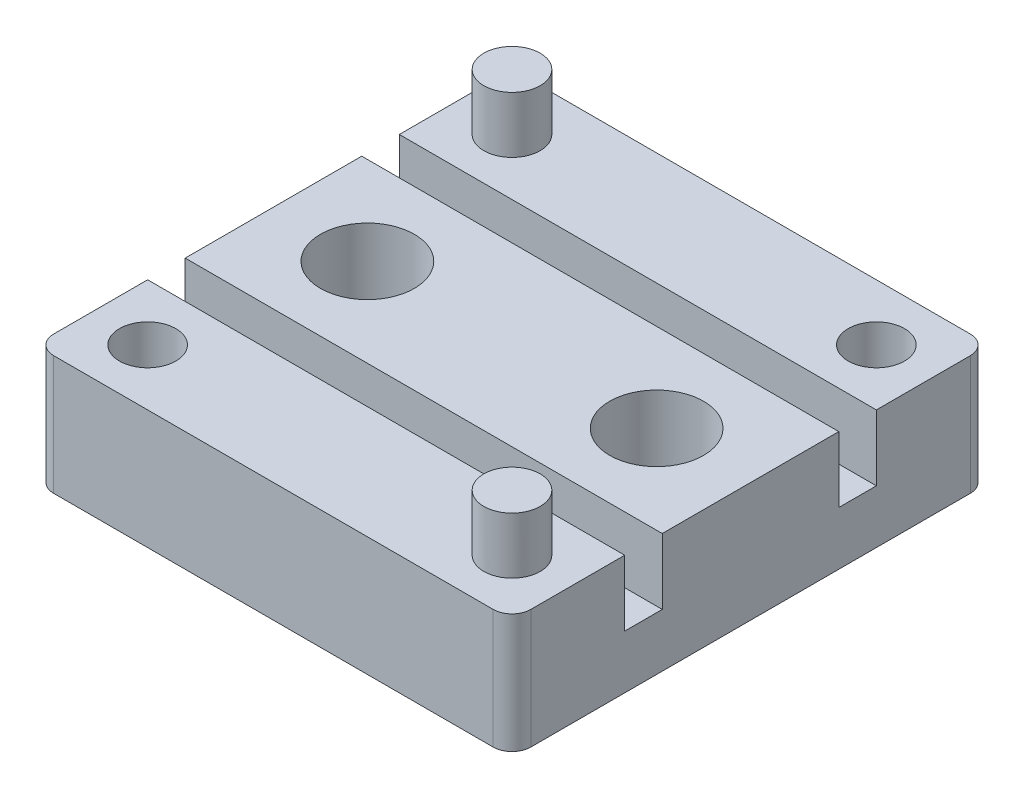
SolidWorks part; units mm, degrees
material "Nylon 101"
ref_plane "Front Plane" through (0, 0, 0) normal (0, 0, 1) x (1, 0, 0)
ref_plane "Top Plane" through (0, 0, 0) normal (0, 1, 0) x (1, 0, 0)
ref_plane "Right Plane" through (0, 0, 0) normal (1, 0, 0) x (0, 0, -1)
sketch "Sketch1" plane through (0, 0, 0) normal (0, 1, 0) x (1, 0, 0)
  line L1 (0, 0) -> (-12.7, 0)
  line L2 (0, 0) -> (0, 12.7)
  line L3 (0, 12.7) -> (-12.7, 12.7)
  line L4 (-12.7, 0) -> (-12.7, 12.7)
  circle A0 centre (-2.5, 6.35) radius 1.25
  circle A1 centre (-10.2, 6.35) radius 1.25
  point P9 (0, 6.35)
  dimension "D3" = 2.5
  dimension "D4" = 2.5
  dimension "D5" = 2.5
  dimension "D1" = 12.7
  dimension "D2" = 12.7
extrude "Boss-Extrude1" add sketch "Sketch1" along normal blind 3.175
sketch "Sketch2" plane through (0, 3.175, 0) normal (0, 1, 0) x (1, 0, 0)
  line L0 (0, 12.7) -> (-12.7, 12.7) construction
  line L1 (-12.7, 12.7) -> (-12.7, 0) construction
  circle A0 centre (-11.2, 11.2) radius 0.75
  dimension "D1" = 1.5
  dimension "D2" = 1.5
  dimension "D3" = 1.5
extrude "Boss-Extrude2" add sketch "Sketch2" along normal blind 1.5
sketch "Sketch3" plane through (0, 3.175, 0) normal (0, 1, 0) x (1, 0, 0)
  line L0 (0, 12.7) -> (-12.7, 12.7) construction
  line L1 (0, 0) -> (0, 12.7) construction
  circle A0 centre (-1.5, 11.2) radius 0.75
  dimension "D1" = 1.5
  dimension "D2" = 1.5
  dimension "D3" = 1.5
extrude "Cut-Extrude1" cut sketch "Sketch3" against normal blind 1.5
ref_plane "Plane2" through (-6.35, 0, -6.35) normal (-0.7071, 0, -0.7071) x (-0.7071, 0, 0.7071)
ref_plane "Plane3" through (0, 0, 0) normal (-0.7071, 0, 0.7071) x (0.7071, 0, 0.7071)
ref_plane "Plane4" through (0, 0, -6.35) normal (0, 0, -1) x (-1, 0, 0)
mirror "Mirror1" about plane through (-6.35, 0, -6.35) normal (-0.7071, 0, -0.7071) of "Boss-Extrude2"
mirror "Mirror2" about plane through (0, 0, 0) normal (-0.7071, 0, 0.7071) of "Cut-Extrude1"
sketch "Sketch4" plane through (0, 3.175, 0) normal (0, 1, 0) x (1, 0, 0)
  line L0 (-12.7, 12.7) -> (-12.7, 0) construction
  line L1 (-12.7, 8.7) -> (0, 8.7)
  line L2 (-12.7, 8.7) -> (-12.7, 9.7)
  line L3 (-12.7, 9.7) -> (0, 9.7)
  line L4 (0, 8.7) -> (0, 9.7)
  line L5 (0, 0) -> (0, 12.7) construction
  line L6 (0, 12.7) -> (-12.7, 12.7) construction
  dimension "D1" = 1
  dimension "D2" = 3
extrude "Cut-Extrude2" cut sketch "Sketch4" against normal blind 1.75
sketch "Sketch5" plane through (0, 1.425, 0) normal (0, 1, 0) x (1, 0, 0)
  line L0 (0, 9.7) -> (-12.7, 9.7) construction
  line L1 (-9.85, 9.7) -> (-2.85, 9.7)
  line L2 (-9.85, 9.7) -> (-9.85, 8.7)
  line L3 (-9.85, 8.7) -> (-2.85, 8.7)
  line L4 (-2.85, 9.7) -> (-2.85, 8.7)
  line L5 (-12.7, 8.7) -> (0, 8.7) construction
  line L6 (-12.7, 9.7) -> (-12.7, 8.7) construction
  dimension "D1" = 7
  dimension "D2" = 2.85
extrude "Cut-Extrude3" cut sketch "Sketch5" against normal blind 0.75
fillet "Fillet1" radius 0.25 4 edges at (-2.85, 0.675, -9.2) (-9.85, 0.675, -9.2) (-9.85, 1.425, -9.2) (-2.85, 1.425, -9.2)
fillet "Fillet2" radius 0.5 4 edges at (-12.7, 1.5875, 0) (0, 1.5875, 0) (0, 1.5875, -12.7) (-12.7, 1.5875, -12.7)
mirror "Mirror3" about plane through (0, 0, -6.35) normal (0, 0, -1) of "Cut-Extrude2", "Cut-Extrude3", "Fillet1"
